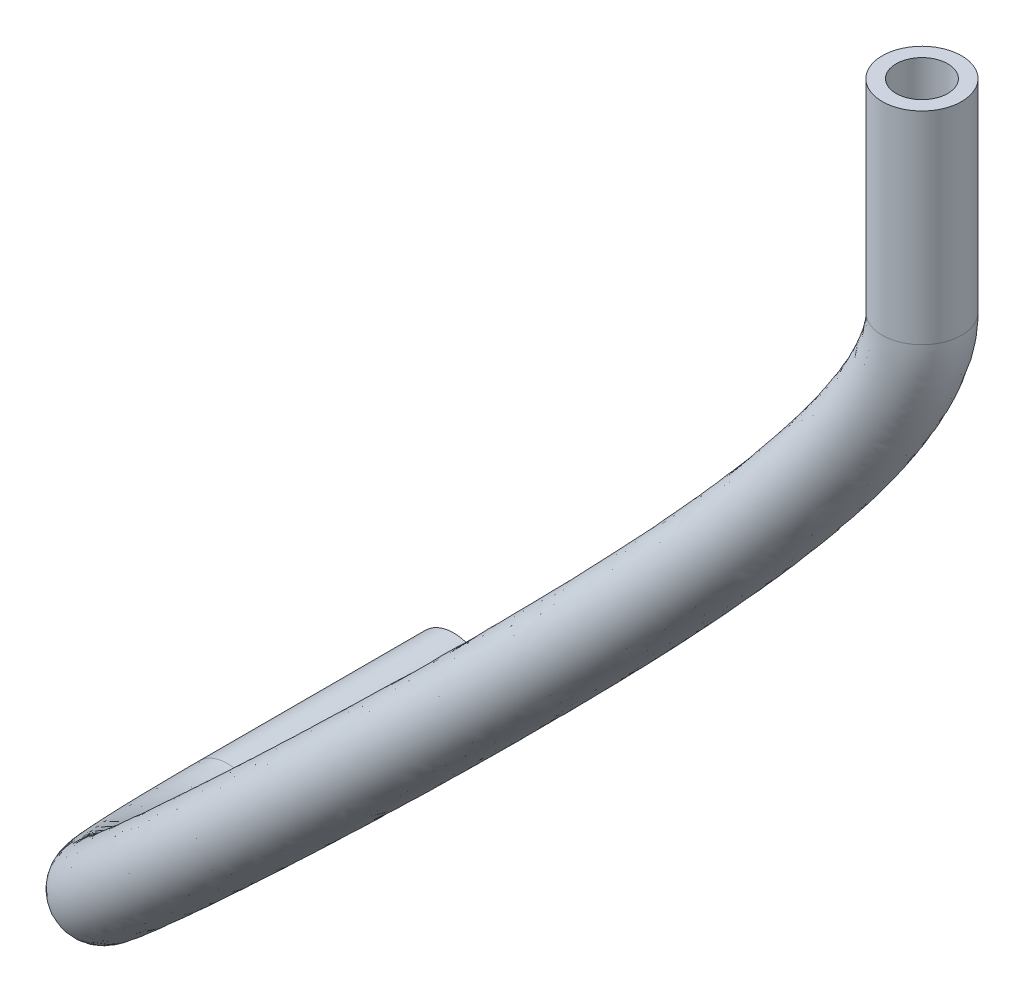
SolidWorks part; units mm, degrees
ref_plane "Front Plane" through (0, 0, 0) normal (0, 0, 1) x (1, 0, 0)
ref_plane "Top Plane" through (0, 0, 0) normal (0, 1, 0) x (1, 0, 0)
ref_plane "Right Plane" through (0, 0, 0) normal (1, 0, 0) x (0, 0, -1)
sketch3d "3DSketch1"
  line L0 (-150.0853, -109.4823, -25.525) -> (-150.0853, -119.6823, -25.525)
  line L1 (-209.2457, -183.0337, -61.0875) -> (-209.2457, -183.0337, -49.6875)
  spline S0 degree 3 poles (-150.0853, -119.6823, -25.525) (-150.0853, -124.3696, -25.525) (-171.1592, -147.7274, -24.6649) (-209.2457, -183.0337, -34.1268) (-209.2457, -183.0337, -49.6875) knots 0 0 0 0 0.428586 1 1 1 1
sketch "Sketch1" plane through (0, 0, -51.4875) normal (0, 0, 1) x (1, 0, 0)
  circle A0 centre (-209.2457, -183.0337) radius 2
  circle A1 centre (-209.2457, -183.0337) radius 3.5524 construction
  circle A2 centre (-209.2457, -183.0337) radius 1.3
  dimension "D1" = 4
  dimension "D2" = 2.6
sweep "Sweep1" add profiles "Sketch1" path "3DSketch1"
